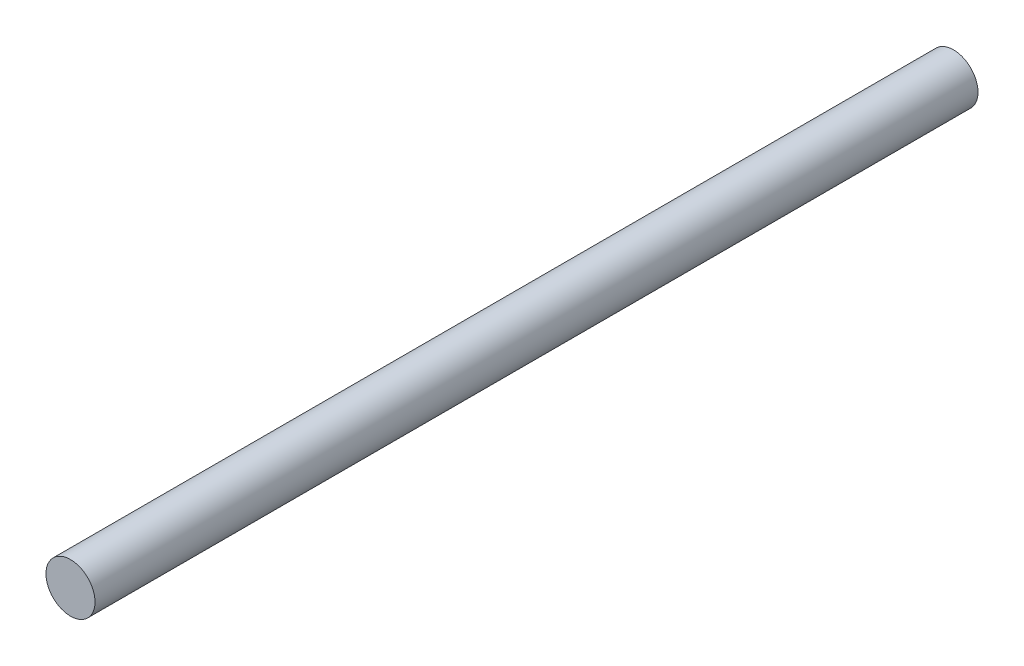
SolidWorks part; units mm, degrees
ref_plane "前视基准面" through (0, 0, 0) normal (0, 0, 1) x (1, 0, 0)
ref_plane "上视基准面" through (0, 0, 0) normal (0, 1, 0) x (1, 0, 0)
ref_plane "右视基准面" through (0, 0, 0) normal (1, 0, 0) x (0, 0, -1)
sketch "草图1" plane through (0, 0, 0) normal (0, 0, 1) x (1, 0, 0)
  circle A0 centre (0, 0) radius 1.25
  dimension "D1" = 2.5
extrude "凸台-拉伸1" add sketch "草图1" along normal blind 45
